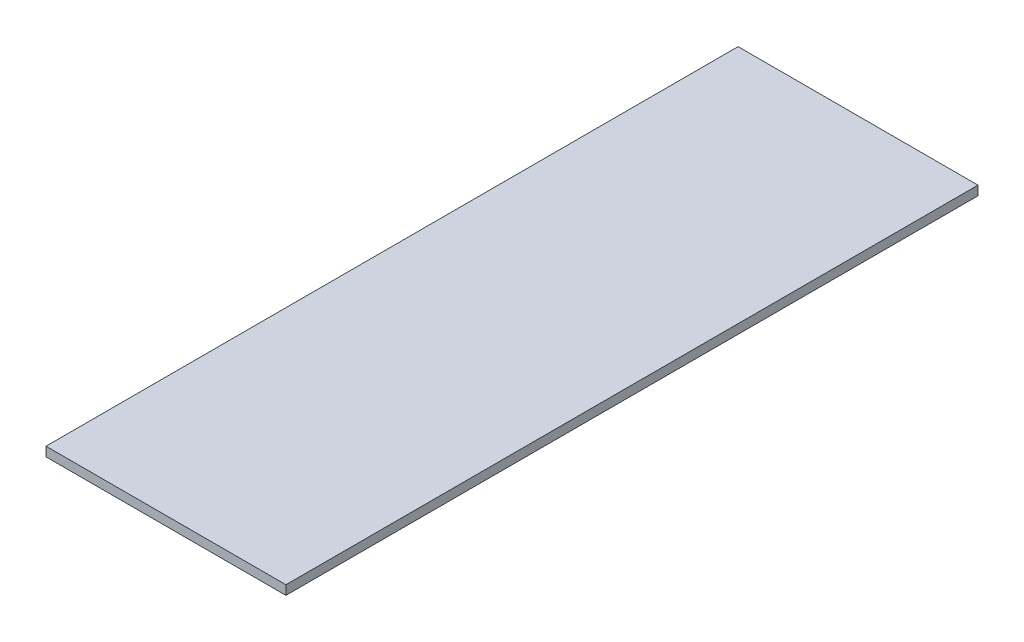
SolidWorks part; units mm, degrees
material "Glass"
ref_plane "Front Plane" through (0, 0, 0) normal (0, 0, 1) x (1, 0, 0)
ref_plane "Top Plane" through (0, 0, 0) normal (0, 1, 0) x (1, 0, 0)
ref_plane "Right Plane" through (0, 0, 0) normal (1, 0, 0) x (0, 0, -1)
sketch "Sketch1" plane through (0, 25.5, 0) normal (0, 1, 0) x (1, 0, 0)
  line L0 (0, 30) -> (0, 30.25)
  line L1 (-13, 30) -> (13, 30)
  line L2 (-13, 30) -> (-13, -45)
  line L3 (-13, -45) -> (13, -45)
  line L4 (13, 30) -> (13, -45)
  line L5 (13.25, 30.25) -> (-13.25, 30.25) construction
  dimension "D1" = 75
  dimension "D2" = 26
  dimension "D3" = 0.25
extrude "Boss-Extrude1" add sketch "Sketch1" along normal blind 1 contours L1 L4 L3 L2
